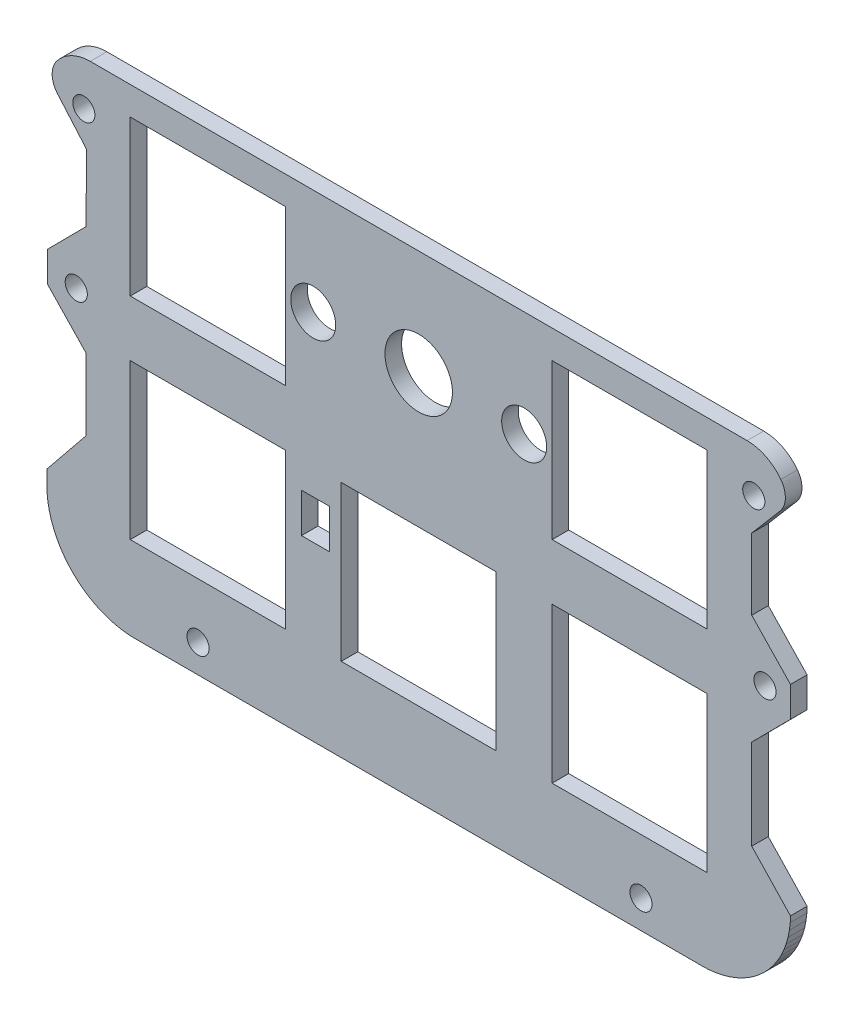
SolidWorks part; units mm, degrees
ref_plane "Front Plane" through (0, 0, 0) normal (0, 0, 1) x (1, 0, 0)
ref_plane "Top Plane" through (0, 0, 0) normal (0, 1, 0) x (1, 0, 0)
ref_plane "Right Plane" through (0, 0, 0) normal (1, 0, 0) x (0, 0, -1)
sketch "Model" plane through (0, 0, 0) normal (0, 0, 1) x (1, 0, 0)
  line L0 (16.6205, 16.7817) -> (2.621, 16.7817)
  line L1 (2.621, 16.7817) -> (2.621, 2.7823)
  line L2 (2.621, 2.7823) -> (16.6205, 2.7823)
  line L3 (16.6205, 2.7823) -> (16.6205, 16.7817)
  line L4 (54.7204, 35.8316) -> (40.7211, 35.8316)
  line L5 (40.7211, 35.8316) -> (40.7211, 21.8323)
  line L6 (40.7211, 21.8323) -> (54.7204, 21.8323)
  line L7 (54.7204, 21.8323) -> (54.7204, 35.8316)
  line L8 (21.671, 16.7817) -> (21.671, 2.7823)
  line L9 (21.671, 2.7823) -> (35.6704, 2.7823)
  line L10 (35.6704, 2.7823) -> (35.6704, 16.7817)
  line L11 (35.6704, 16.7817) -> (21.671, 16.7817)
  line L12 (16.6205, 21.8323) -> (16.6205, 35.8316)
  line L13 (16.6205, 35.8316) -> (2.621, 35.8316)
  line L14 (2.621, 35.8316) -> (2.621, 21.8323)
  line L15 (2.621, 21.8323) -> (16.6205, 21.8323)
  line L16 (40.7211, 16.7817) -> (40.7211, 2.7823)
  line L17 (40.7211, 2.7823) -> (54.7204, 2.7823)
  line L18 (54.7204, 2.7823) -> (54.7204, 16.7817)
  line L19 (54.7204, 16.7817) -> (40.7211, 16.7817)
  line L20 (-0.9935, 38.3789) -> (58.326, 38.3789)
  line L21 (62.2453, 3.1661) -> (62.2262, 2.6367)
  line L22 (62.2262, 2.6367) -> (62.1524, 2.0114)
  line L23 (62.1524, 2.0114) -> (62.0292, 1.3849)
  line L24 (62.0292, 1.3849) -> (61.8553, 0.7766)
  line L25 (61.8553, 0.7766) -> (61.6442, 0.2027)
  line L26 (61.6442, 0.2027) -> (61.3794, -0.3764)
  line L27 (61.3794, -0.3764) -> (61.0647, -0.9348)
  line L28 (61.0647, -0.9348) -> (60.7212, -1.4467)
  line L29 (60.7212, -1.4467) -> (60.333, -1.9414)
  line L30 (60.333, -1.9414) -> (59.9058, -2.4019)
  line L31 (59.9058, -2.4019) -> (59.4459, -2.8288)
  line L32 (59.4459, -2.8288) -> (58.9476, -3.2204)
  line L33 (58.9476, -3.2204) -> (58.4345, -3.5634)
  line L34 (58.4345, -3.5634) -> (57.8802, -3.876)
  line L35 (57.8802, -3.876) -> (57.3021, -4.1405)
  line L36 (57.3021, -4.1405) -> (56.7262, -4.3529)
  line L37 (56.7262, -4.3529) -> (56.116, -4.5268)
  line L38 (56.116, -4.5268) -> (55.4922, -4.6494)
  line L39 (55.4922, -4.6494) -> (54.8784, -4.7221)
  line L40 (54.8784, -4.7221) -> (54.3469, -4.7437)
  line L41 (54.3469, -4.7437) -> (2.9928, -4.7437)
  line L42 (2.9928, -4.7437) -> (2.4645, -4.7221)
  line L43 (2.4645, -4.7221) -> (1.8472, -4.6494)
  line L44 (1.8472, -4.6494) -> (1.2235, -4.5262)
  line L45 (1.2235, -4.5262) -> (0.6156, -4.353)
  line L46 (0.6156, -4.353) -> (0.0383, -4.1402)
  line L47 (0.0383, -4.1402) -> (-0.5328, -3.8785)
  line L48 (-0.5328, -3.8785) -> (-1.0889, -3.5671)
  line L49 (-1.0889, -3.5671) -> (-1.6146, -3.2154)
  line L50 (-1.6146, -3.2154) -> (-2.1023, -2.8297)
  line L51 (-2.1023, -2.8297) -> (-2.5583, -2.4098)
  line L52 (-2.5583, -2.4098) -> (-2.9923, -1.9422)
  line L53 (-2.9923, -1.9422) -> (-3.3906, -1.4349)
  line L54 (-3.3906, -1.4349) -> (-3.7304, -0.9216)
  line L55 (-3.7304, -0.9216) -> (-4.0368, -0.378)
  line L56 (-4.0368, -0.378) -> (-4.2957, 0.1871)
  line L57 (-4.2957, 0.1871) -> (-4.5168, 0.7768)
  line L58 (-4.5168, 0.7768) -> (-4.6871, 1.3875)
  line L59 (-4.6871, 1.3875) -> (-4.8133, 2.0111)
  line L60 (-4.8133, 2.0111) -> (-4.8839, 2.6392)
  line L61 (-4.8839, 2.6392) -> (-4.9049, 3.156)
  line L62 (-4.9049, 3.156) -> (-4.9049, 4.5385)
  line L63 (62.2459, 21.2672) -> (58.746, 24.9291)
  line L64 (61.3046, 34.3553) -> (58.7462, 31.3582)
  line L65 (62.2456, 18.5347) -> (58.7457, 15.0073)
  line L66 (62.2453, 3.1661) -> (58.7454, 6.8644)
  line L67 (62.2459, 21.2672) -> (62.2456, 18.5347)
  line L68 (58.7462, 31.3582) -> (58.746, 24.9291)
  line L69 (58.7457, 15.0073) -> (58.7454, 6.8644)
  line L70 (-1.363, 8.918) -> (-1.3593, 15.3639)
  line L71 (-4.9049, 4.5385) -> (-1.363, 8.918)
  line L72 (-4.8537, 19.0201) -> (-1.3536, 15.3581)
  line L73 (-4.8537, 19.0201) -> (-4.8534, 21.7526)
  line L74 (-4.8534, 21.7526) -> (-1.3535, 25.2801)
  line L75 (-1.3535, 25.2801) -> (-1.35, 31.36)
  line L76 (-3.9434, 34.357) -> (-1.35, 31.36)
  line L77 (18.084, 10.8243) -> (20.624, 10.8243)
  line L78 (20.624, 10.8243) -> (20.624, 14.3803)
  line L79 (20.624, 14.3803) -> (18.084, 14.3803)
  line L80 (18.084, 14.3803) -> (18.084, 10.8243)
  circle A0 centre (38.1958, 28.832) radius 2.032
  circle A1 centre (19.1458, 28.832) radius 2.032
  circle A2 centre (28.6708, 28.832) radius 3.048
  circle A3 centre (-2.2555, 20.0102) radius 1
  circle A4 centre (58.9312, 34.3808) radius 1
  circle A5 centre (59.9445, 20.0102) radius 1
  circle A6 centre (8.7445, -2.1898) radius 1
  circle A7 centre (48.7445, -2.1898) radius 1
  circle A8 centre (-1.5688, 34.3808) radius 1
  arc A9 (-0.9935, 38.3789) -> (-4.0236, 36.8756) centre (-0.9935, 34.5737) ccw
  arc A10 (61.3786, 36.8602) -> (58.326, 38.3789) centre (58.326, 34.5517) ccw
  arc A11 (61.3046, 34.3553) -> (61.3786, 36.8602) centre (59.7834, 35.6538) ccw
  arc A12 (-4.0236, 36.8756) -> (-3.9434, 34.357) centre (-2.431, 35.6657) ccw
extrude "凸台-拉伸1" add sketch "Model" along normal blind 1.5
